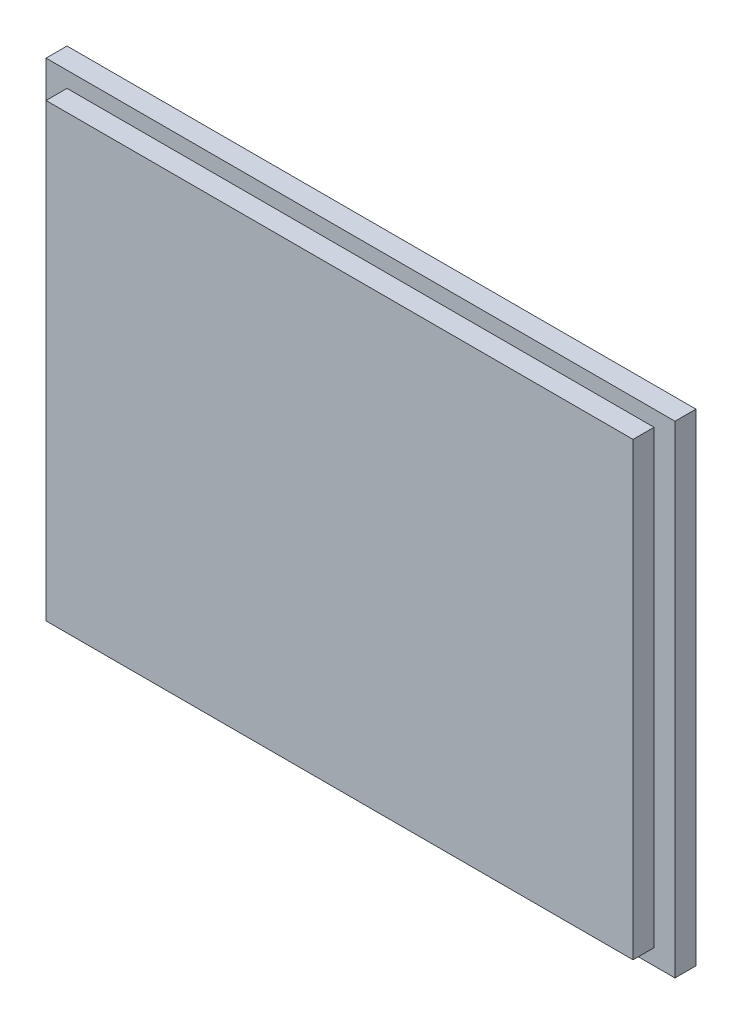
SolidWorks part; units mm, degrees
ref_plane "Plano frontal" through (0, 0, 0) normal (0, 0, 1) x (1, 0, 0)
ref_plane "Plano superior" through (0, 0, 0) normal (0, 1, 0) x (1, 0, 0)
ref_plane "Plano direito" through (0, 0, 0) normal (1, 0, 0) x (0, 0, -1)
sketch "Esboço1" plane through (0, 0, 0) normal (0, 0, 1) x (1, 0, 0)
  line L1 (-150, 115) -> (150, 115)
  line L2 (-150, 115) -> (-150, -115)
  line L3 (-150, -115) -> (150, -115)
  line L4 (150, 115) -> (150, -115)
  line L5 (-150, 115) -> (150, -115) construction
  line L6 (-150, -115) -> (150, 115) construction
  point P0 (0, 0)
extrude "Ressalto-extrusão1" add sketch "Esboço1" along normal blind 10
sketch "Esboço2" plane through (0, 0, 10) normal (0, 0, 1) x (1, 0, 0)
  line L1 (-140, -107.5) -> (140, -107.5)
  line L2 (-140, -107.5) -> (-140, 107.5)
  line L3 (-140, 107.5) -> (140, 107.5)
  line L4 (140, -107.5) -> (140, 107.5)
  line L5 (-140, -107.5) -> (140, 107.5) construction
  line L6 (-140, 107.5) -> (140, -107.5) construction
  point P0 (0, 0)
extrude "Ressalto-extrusão2" add sketch "Esboço2" along normal blind 10
